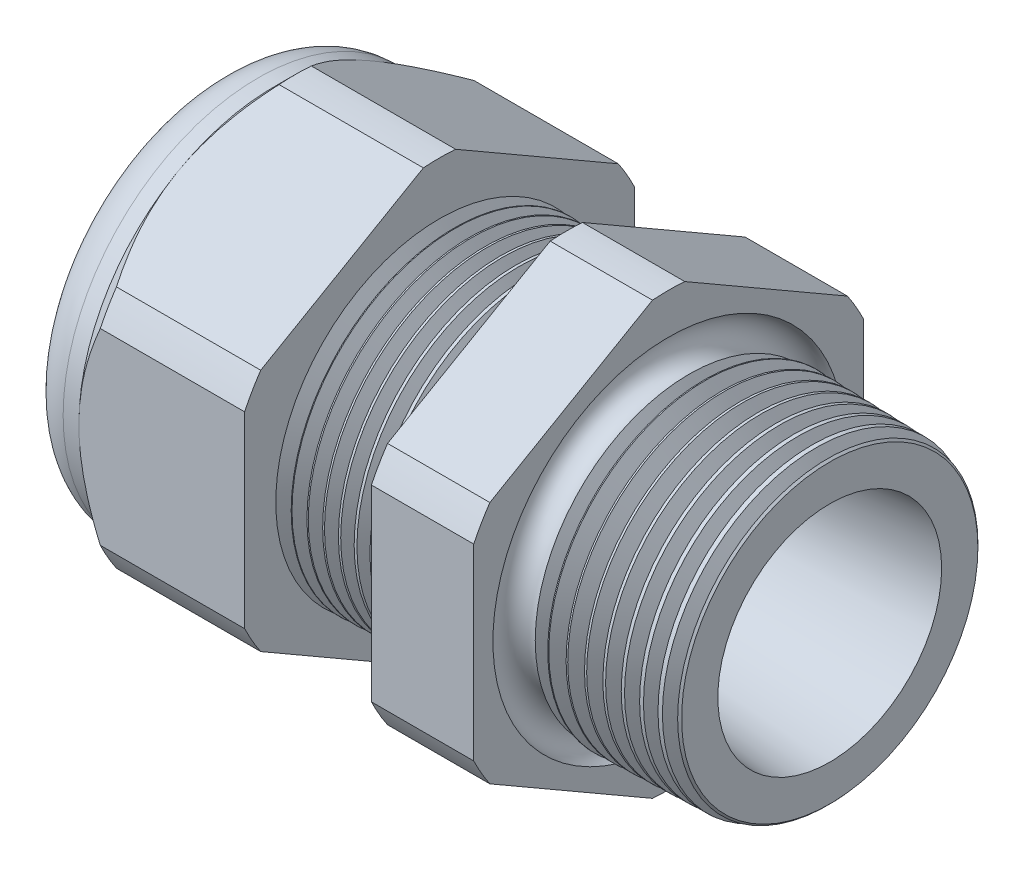
SolidWorks part; units mm, degrees
ref_plane "Front Plane" through (0, 0, 0) normal (0, 0, 1) x (1, 0, 0)
ref_plane "Top Plane" through (0, 0, 0) normal (0, 1, 0) x (1, 0, 0)
ref_plane "Right Plane" through (0, 0, 0) normal (1, 0, 0) x (0, 0, -1)
sketch "Sketch10" plane through (0, 0, 0) normal (0, 0, 1) x (1, 0, 0)
  line L0 (0, 0) -> (-115.3565, 0) construction
  line L1 (-29.972, 3.937) -> (-19.072, 3.937)
  line L2 (0, 5.4696) -> (0, 7.5016)
  line L3 (-7.874, 7.7078) -> (0, 7.5016)
  line L4 (-7.874, 19.05) -> (-7.874, 7.7078)
  line L5 (-7.874, 19.05) -> (-12.874, 19.05)
  line L6 (-12.874, 19.05) -> (-12.874, 7.8387)
  line L7 (-19.072, 8.001) -> (-12.874, 7.8387)
  line L8 (-19.072, 8.001) -> (-19.072, 19.05)
  line L9 (-19.072, 19.05) -> (-27.172, 19.05)
  line L10 (-27.172, 19.05) -> (-27.172, 9.525)
  line L11 (-27.172, 9.525) -> (-29.972, 9.525)
  line L12 (-29.972, 9.525) -> (-29.972, 3.937)
  line L13 (-19.072, 3.937) -> (0, 5.4696)
  dimension "D1" = 29.972
  dimension "D2" = 7.874
  dimension "D3" = 1.5
  dimension "D4" = 2.032
  dimension "A" = 16.002
  dimension "D6" = 19.05
  dimension "D8" = 38.1
  dimension "D9" = 2.8
  dimension "D10" = 8.1
  dimension "D11" = 5
  dimension "D" = 7.874
revolve "Revolve2" add sketch "Sketch10" angle 360 about L0
sketch "Sketch12" plane through (-27.172, 0, 0) normal (-1, 0, 0) x (0, 0, 1)
  line L1 (-0.7885, 10.5433) -> (-8.7365, 5.9545)
  line L2 (-9.525, 4.5888) -> (-9.525, -4.5888)
  line L3 (-8.7365, -5.9545) -> (-0.7885, -10.5433)
  line L4 (0.7885, -10.5433) -> (8.7365, -5.9545)
  line L5 (9.525, -4.5888) -> (9.525, 4.5888)
  line L6 (8.7365, 5.9545) -> (0.7885, 10.5433)
  circle A0 centre (0, 0) radius 9.525 construction
  arc A1 (0.7885, 10.5433) -> (-0.7885, 10.5433) centre (0, 0) ccw
  arc A2 (-8.7365, 5.9545) -> (-9.525, 4.5888) centre (0, 0) ccw
  arc A3 (-9.525, -4.5888) -> (-8.7365, -5.9545) centre (0, 0) ccw
  arc A4 (-0.7885, -10.5433) -> (0.7885, -10.5433) centre (0, 0) ccw
  arc A5 (8.7365, -5.9545) -> (9.525, -4.5888) centre (0, 0) ccw
  arc A6 (9.525, 4.5888) -> (8.7365, 5.9545) centre (0, 0) ccw
  dimension "D2" = 21.1455
  dimension "D1" = 19.05
extrude "Cut-Extrude2" cut sketch "Sketch12" against normal through all flip side to cut
fillet "Fillet4" radius 2.032 1 edges at (-29.972, 0, -9.525)
sketch "Sketch19" plane through (-27.172, 0, 0) normal (-1, 0, 0) x (0, 0, 1)
  line L0 (9.525, 0) -> (9.525, 4.5888) construction
  circle A0 centre (0, 0) radius 9.525
extrude "Cut-Extrude3" cut sketch "Sketch19" against normal blind 2 draft 45 flip side to cut
chamfer "Chamfer1" distance 0.254 angle 45 1 edges at (0, 0, -7.5016)
sketch "Sketch21" plane through (-29.972, 0, 0) normal (-1, 0, 0) x (0, 0, 1)
  circle A0 centre (0, 0) radius 3.937
  circle A2 centre (0, 0) radius 3.937 construction
extrude "plug" add sketch "Sketch21" against normal blind 3.81 separate body
sketch "Sketch22" plane through (-29.972, 0, 0) normal (-1, 0, 0) x (0, 0, 1)
  circle A0 centre (0, 0) radius 3.683
  circle A1 centre (0, 0) radius 3.937 construction
  dimension "D1" = 0.254
extrude "Cut-Extrude4" cut sketch "Sketch22" against normal blind 0.508
sketch "Sketch27" plane through (-29.464, 0, 0) normal (-1, 0, 0) x (0, 0, 1)
  line L0 (-4.3624, 0) -> (4.3624, 0) construction
  circle A0 centre (-2.7904, 0) radius 0.889
  circle A1 centre (0, 0) radius 3.683 construction
  dimension "D1" = 0.0036
  dimension "holedia" = 1.778
extrude "plugholes" cut sketch "Sketch27" against normal through all
pattern_circular "CirPattern1" count 3 over 360 about axis through (0, 0, 0) along (1, 0, 0) of "plugholes"
sketch "Sketch28" [suppressed] plane through (-29.464, 0, 0) normal (-1, 0, 0) x (0, 0, 1)
  circle A0 centre (0, 0) radius 0.762
  dimension "midholedia" = 1.778
extrude "midhole" [suppressed] cut sketch "Sketch28" against normal through all
sketch "Sketch29" plane through (0, 0, 0) normal (0, 0, 1) x (1, 0, 0)
  line L0 (-19.072, 8.001) -> (-18.339, 7.9818)
  line L1 (-12.874, 7.8387) -> (-19.072, 8.001) construction
  line L2 (-18.339, 7.9818) -> (-18.7221, 7.3566)
  line L3 (-18.7221, 7.3566) -> (-19.072, 8.001)
  dimension "D1" = 60
  dimension "D2" = 60
  dimension "D3" = 0.635
revolve "Cut-Revolve1" cut sketch "Sketch29" angle 360 about axis through (0, 0, 0) along (-1, 0, 0)
pattern_linear "LPattern1" count 8 spacing 0.762 along (1, 0, 0) of "Cut-Revolve1"
sketch "Sketch30" plane through (0, 0, 0) normal (0, 0, 1) x (1, 0, 0)
  line L0 (-7.874, 7.7078) -> (-6.9944, 7.6847)
  line L1 (-7.874, 10.5433) -> (-7.874, 5.9545) construction
  line L2 (-0.2539, 7.5082) -> (-7.874, 7.7078) construction
  line L3 (-6.9944, 7.6847) -> (-7.4542, 6.9345)
  line L4 (-7.4542, 6.9345) -> (-7.874, 7.7078)
  dimension "D1" = 60
  dimension "D2" = 60
  dimension "D3" = 0.762
revolve "Cut-Revolve2" cut sketch "Sketch30" angle 360 about axis through (0, 0, 0) along (-1, 0, 0)
pattern_linear "LPattern2" count 9 spacing 0.889 along (1, 0, 0) of "Cut-Revolve2"
sketch "Sketch31" [suppressed] plane through (-38.354, 0, 0) normal (-1, 0, 0) x (0, 0, 1)
  line L0 (-1.905, 1.905) -> (1.905, 1.905)
  line L1 (-1.905, -1.905) -> (1.905, -1.905)
  circle A0 centre (0, 0) radius 1.905 construction
  arc A1 (-1.905, 1.905) -> (-1.905, -1.905) centre (-1.905, 0) ccw
  arc A2 (1.905, 1.905) -> (1.905, -1.905) centre (1.905, 0) cw
extrude "Cut-Extrude5" [suppressed] cut sketch "Sketch31" against normal through all
sketch "Sketch32" plane through (0, 0, 0) normal (0, 0, 1) x (1, 0, 0)
  line L0 (-7.874, 10.5433) -> (-7.874, 5.9545) construction
  circle A0 centre (-7.747, 7.7078) radius 0.889
  dimension "D2" = 1.778
  dimension "D1" = 0.127
revolve "Cut-Revolve3" cut sketch "Sketch32" angle 360 about axis through (0, 0, 0) along (-1, 0, 0)
